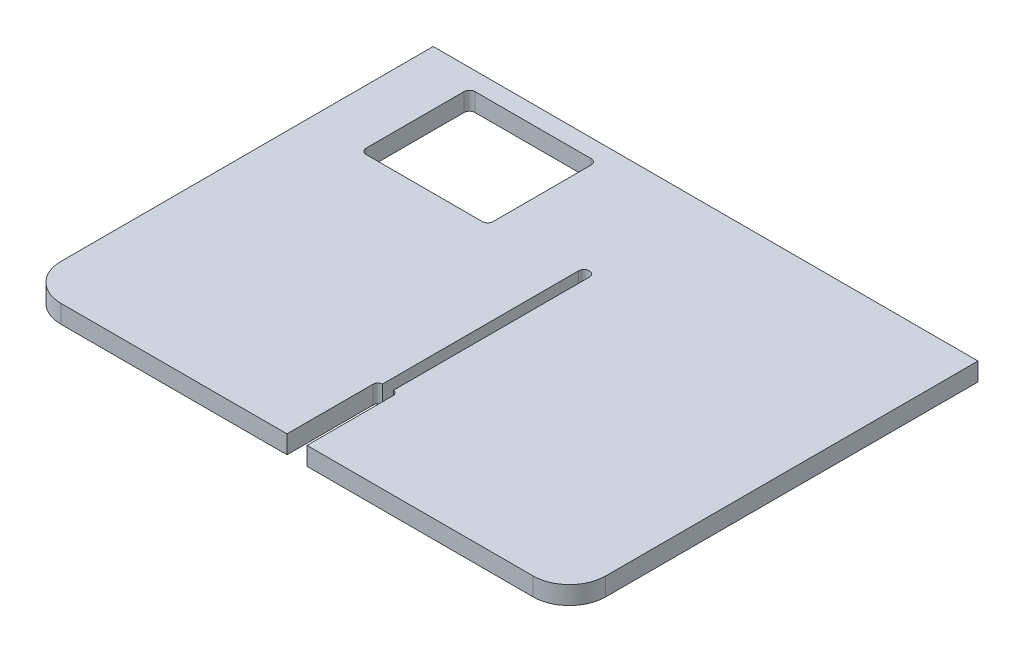
SolidWorks part; units mm, degrees
ref_plane "Ebene vorne" through (0, 0, 0) normal (0, 0, 1) x (1, 0, 0)
ref_plane "Ebene oben" through (0, 0, 0) normal (0, 1, 0) x (1, 0, 0)
ref_plane "Ebene rechts" through (0, 0, 0) normal (1, 0, 0) x (0, 0, -1)
sketch "Skizze1" plane through (0, 0, 0) normal (0, 1, 0) x (1, 0, 0)
  line L0 (150, 75) -> (150, 150)
  line L1 (0, -75) -> (150, -75)
  line L2 (0, -75) -> (0, 75)
  line L3 (150, 150) -> (0, 150)
  line L4 (150, -75) -> (150, 75)
  line L5 (0, 150) -> (0, 75)
  line L6 (0, 0) -> (150, 0) construction
  dimension "D1" = 150
  dimension "D2" = 75
extrude "Linear austragen1" add sketch "Skizze1" along normal blind 10
fillet "Verrundung1" radius 20 1 edges at (150, 5, 75)
mirror "Spiegeln2" about plane through (0, 10, -150) normal (1, 0, 0) of "Verrundung1", "Linear austragen1"
sketch "Skizze3" plane through (0, 0, 0) normal (0, 1, 0) x (-1, 0, 0)
  line L1 (120, -140) -> (50, -140)
  line L2 (120, -140) -> (120, -80)
  line L3 (120, -80) -> (50, -80)
  line L4 (50, -140) -> (50, -80)
  line L8 (150, 55) -> (150, -150) construction
  line L9 (-150, -150) -> (150, -150) construction
  dimension "D1" = 30
  dimension "D2" = 10
  dimension "D3" = 70
  dimension "D4" = 60
extrude "Schnitt-Linear austragen1" cut sketch "Skizze3" along normal through all
fillet "Verrundung2" radius 3 4 edges at (-120, 5, -80) (-50, 5, -80) (-120, 5, -140) (-50, 5, -140)
sketch "Skizze4" plane through (0, 0, 0) normal (0, -1, 0) x (1, 0, 0)
  line L0 (-3, 25) -> (-3, -83)
  line L1 (3, 25) -> (3, -83)
  line L2 (0, 0) -> (-3, 0) construction
  line L3 (0, 0) -> (3, 0) construction
  line L4 (-3, 25) -> (3, 25) construction
  line L5 (-5.5241, 27.5241) -> (-5.5241, 75)
  line L7 (-117, -80) -> (-53, -80) construction
  line L8 (-130, 75) -> (130, 75) construction
  line L10 (5.4759, 27.4759) -> (5.4759, 75)
  line L11 (5.4759, 75) -> (-5.5241, 75)
  arc A0 (-3, 25) -> (-5.5241, 27.5241) centre (-3, 27.5241) cw
  arc A1 (-3, -83) -> (3, -83) centre (0, -83) ccw
  arc A2 (5.4759, 27.4759) -> (3, 25) centre (3, 27.4759) cw
  dimension "D2" = 3
  dimension "D1" = 6
  dimension "D3" = 50
  dimension "D4" = 11
extrude "Schnitt-Linear austragen2" cut sketch "Skizze4" against normal blind 10
